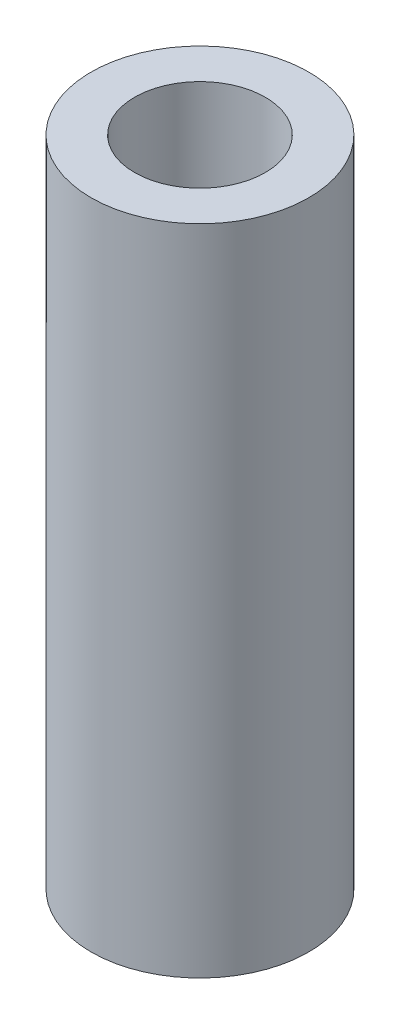
SolidWorks part; units mm, degrees
ref_plane "Front Plane" through (0, 0, 0) normal (0, 0, 1) x (1, 0, 0)
ref_plane "Top Plane" through (0, 0, 0) normal (0, 1, 0) x (1, 0, 0)
ref_plane "Right Plane" through (0, 0, 0) normal (1, 0, 0) x (0, 0, -1)
sketch "Sketch1" plane through (0, 0, 0) normal (0, 1, 0) x (1, 0, 0)
  circle A0 centre (0, 0) radius 2.5
  circle A1 centre (0, 0) radius 1.5
  dimension "D1" = 3
  dimension "D2" = 1
extrude "Boss-Extrude1" add sketch "Sketch1" along normal blind 15 contours A0 A1
equation "\"TABH\"=3"
equation "\"D1@Sketch1\"=\"TABH\""
equation "\"T\"=1"
equation "\"D2@Sketch1\"=\"T\""
